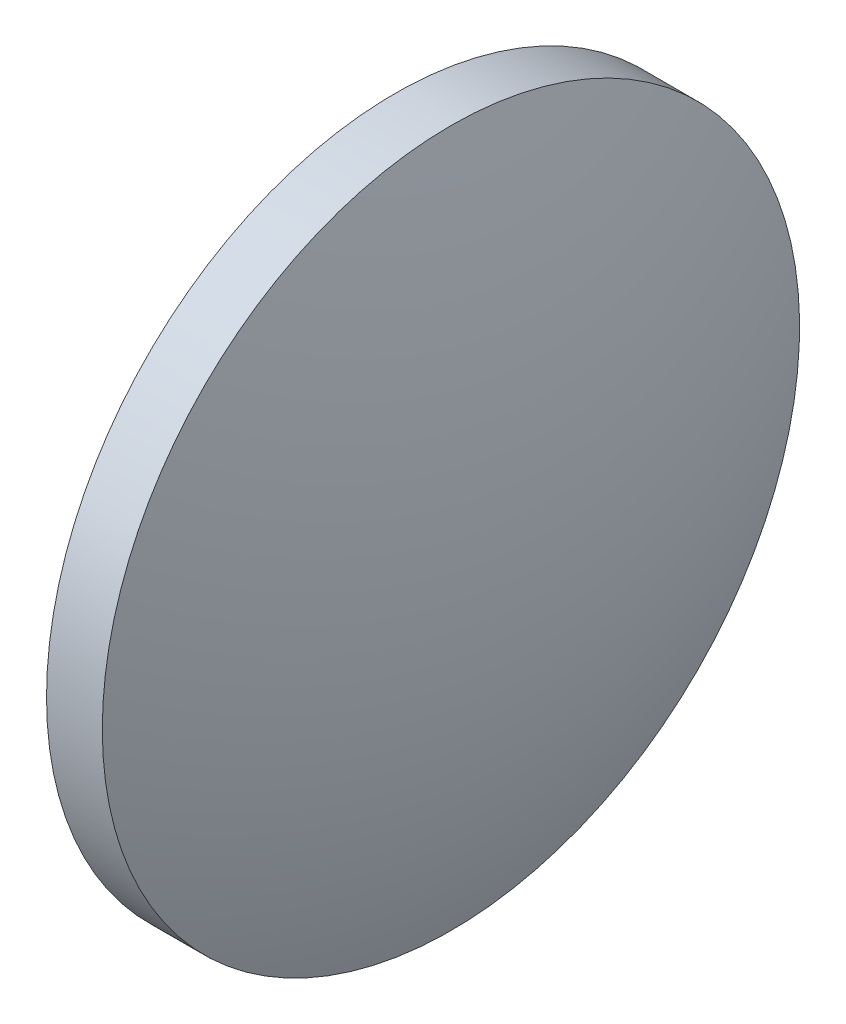
SolidWorks part; units mm, degrees
ref_plane "前视基准面" through (0, 0, 0) normal (0, 0, 1) x (1, 0, 0)
ref_plane "上视基准面" through (0, 0, 0) normal (0, 1, 0) x (1, 0, 0)
ref_plane "右视基准面" through (0, 0, 0) normal (1, 0, 0) x (0, 0, -1)
sketch "草图1" plane through (0, 0, 0) normal (0, 0, 1) x (1, 0, 0)
  line L0 (362.1291, 381.2278) -> (371.5271, 381.2278) construction
  line L1 (364.97, 381.2278) -> (364.97, 388.7278)
  line L2 (364.97, 388.7278) -> (366.17, 388.7278)
  line L3 (367.57, 381.2278) -> (364.97, 381.2278)
  arc A0 (367.57, 381.2278) -> (366.17, 388.7278) centre (346.7807, 381.2278) ccw
revolve "旋转1" add sketch "草图1" angle 360 about L0
